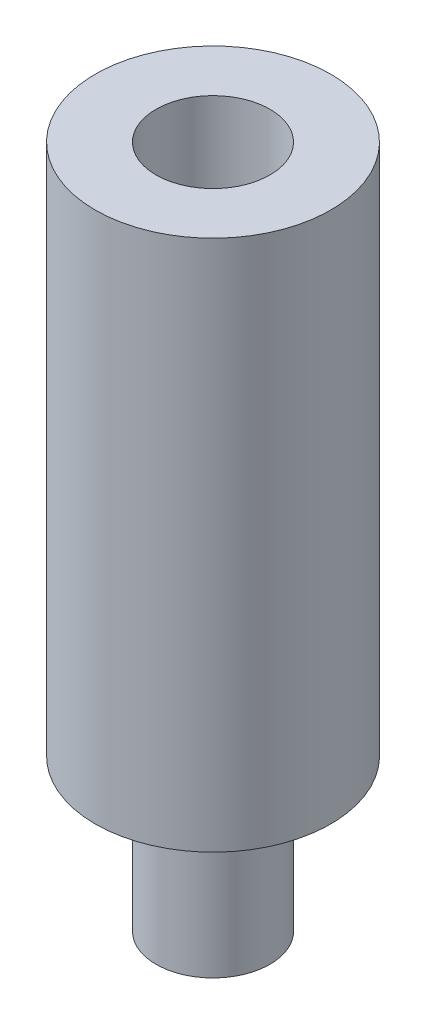
SolidWorks part; units mm, degrees
ref_plane "Front Plane" through (0, 0, 0) normal (0, 0, 1) x (1, 0, 0)
ref_plane "Top Plane" through (0, 0, 0) normal (0, 1, 0) x (1, 0, 0)
ref_plane "Right Plane" through (0, 0, 0) normal (1, 0, 0) x (0, 0, -1)
sketch "Sketch1" plane through (0, 0, 0) normal (0, 1, 0) x (1, 0, 0)
  circle A0 centre (0, 0) radius 3.1
  dimension "D1" = 6.2
extrude "Boss-Extrude1" add sketch "Sketch1" along normal blind 14
sketch "Sketch2" plane through (0, 14, 0) normal (0, 1, 0) x (1, 0, 0)
  circle A0 centre (0, 0) radius 1.5
  dimension "D1" = 3
extrude "Cut-Extrude1" cut sketch "Sketch2" against normal blind 5
sketch "Sketch3" plane through (0, 0, 0) normal (0, -1, 0) x (1, 0, 0)
  circle A0 centre (0, 0) radius 1.5
  dimension "D1" = 3
extrude "Boss-Extrude2" add sketch "Sketch3" along normal blind 4
